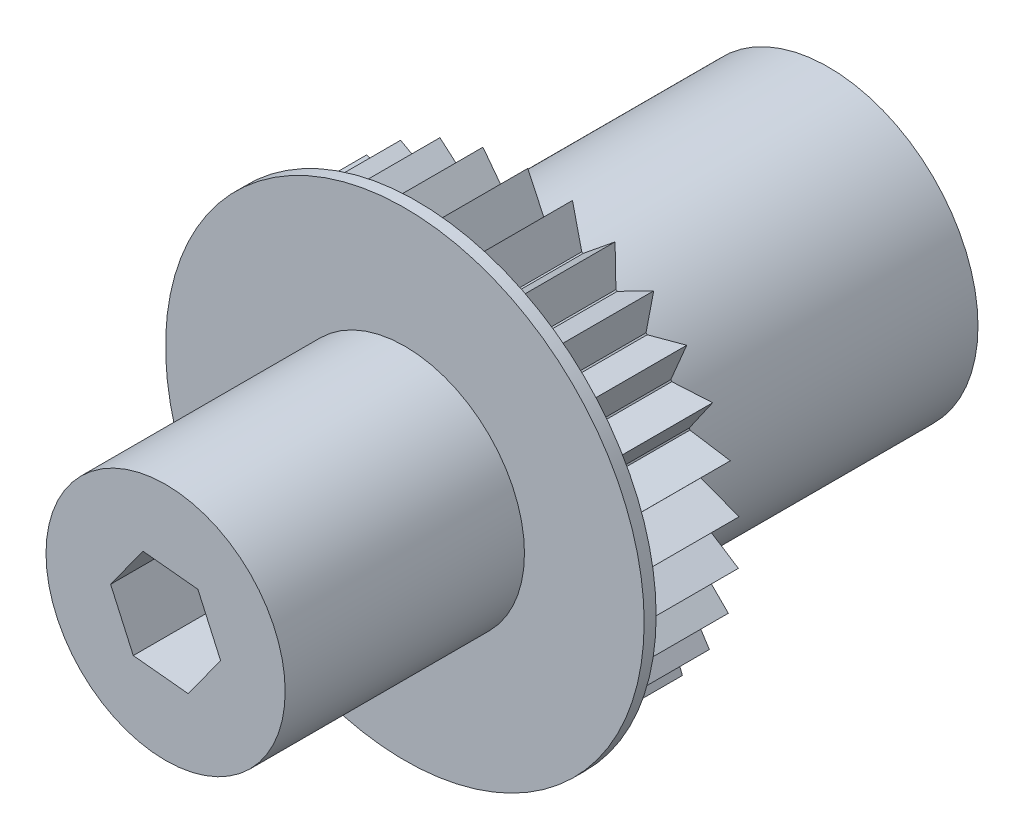
SolidWorks part; units mm, degrees
ref_plane "Front Plane" through (0, 0, 0) normal (0, 0, 1) x (1, 0, 0)
ref_plane "Top Plane" through (0, 0, 0) normal (0, 1, 0) x (1, 0, 0)
ref_plane "Right Plane" through (0, 0, 0) normal (1, 0, 0) x (0, 0, -1)
sketch "Sketch1" plane through (0, 0, 0) normal (0, 0, 1) x (1, 0, 0)
  circle A0 centre (0, 0) radius 12.5
  dimension "D1" = 25
extrude "Boss-Extrude1" add sketch "Sketch1" along normal blind 25.4
sketch "Sketch2" plane through (0, 0, 25.4) normal (0, 0, 1) x (1, 0, 0)
  circle A0 centre (0, 0) radius 9.9949
  dimension "D1" = 19.9898
extrude "Boss-Extrude2" add sketch "Sketch2" along normal blind 30
sketch "Sketch4" plane through (0, 0, 25.4) normal (0, 0, 1) x (1, 0, 0)
  line L0 (0.2712, 17.998) -> (1.7248, 14.9005)
  line L1 (-1.2752, 14.9457) -> (0.2712, 17.998)
  line L2 (1.8601, 14.8842) -> (4.0072, 17.5483)
  line L3 (4.0072, 17.5483) -> (4.7851, 14.2163)
  line L4 (4.914, 14.1722) -> (7.5681, 16.3317)
  line L5 (7.5681, 16.3317) -> (7.6363, 12.9107)
  line L6 (7.7532, 12.8408) -> (10.7983, 14.4013)
  line L7 (10.7983, 14.4013) -> (10.1537, 11.0409)
  line L8 (10.2536, 10.9483) -> (13.5565, 11.8415)
  line L9 (13.5565, 11.8415) -> (12.2274, 8.6886)
  line L10 (12.3058, 8.5772) -> (15.7223, 8.7641)
  line L11 (15.7223, 8.7641) -> (13.7666, 5.9565)
  line L12 (13.8202, 5.8312) -> (17.2009, 5.3038)
  line L13 (17.2009, 5.3038) -> (14.7042, 2.9641)
  line L14 (14.7305, 2.8304) -> (17.9277, 1.6116)
  line L15 (17.9277, 1.6116) -> (14.9992, -0.1579)
  line L16 (14.9971, -0.2941) -> (17.871, -2.151)
  line L17 (17.871, -2.151) -> (14.6386, -3.2729)
  line L18 (14.6083, -3.4057) -> (17.0333, -5.8196)
  line L19 (17.0333, -5.8196) -> (13.6382, -6.2449)
  line L20 (13.5809, -6.3685) -> (15.4511, -9.2338)
  line L21 (15.4511, -9.2338) -> (12.0418, -8.944)
  line L22 (11.9601, -9.053) -> (13.1936, -12.2445)
  line L23 (13.1936, -12.2445) -> (9.9191, -11.2522)
  line L24 (9.8165, -11.3418) -> (10.3596, -14.72)
  line L25 (10.3596, -14.72) -> (7.3629, -13.0686)
  line L26 (7.2439, -13.1349) -> (7.0727, -16.5522)
  line L27 (7.0727, -16.5522) -> (4.4849, -14.3138)
  line L28 (4.3547, -14.354) -> (3.4767, -17.661)
  line L29 (3.4767, -17.661) -> (1.4108, -14.9335)
  line L30 (1.2752, -14.9457) -> (-0.2712, -17.998)
  line L31 (-0.2712, -17.998) -> (-1.7248, -14.9005)
  line L32 (-1.8601, -14.8842) -> (-4.0072, -17.5483)
  line L33 (-4.0072, -17.5483) -> (-4.7851, -14.2163)
  line L34 (-4.914, -14.1722) -> (-7.5681, -16.3317)
  line L35 (-7.5681, -16.3317) -> (-7.6363, -12.9107)
  line L36 (-7.7532, -12.8408) -> (-10.7983, -14.4013)
  line L37 (-10.7983, -14.4013) -> (-10.1537, -11.0409)
  line L38 (-10.2536, -10.9483) -> (-13.5565, -11.8415)
  line L39 (-13.5565, -11.8415) -> (-12.2274, -8.6886)
  line L40 (-12.3058, -8.5772) -> (-15.7223, -8.7641)
  line L41 (-15.7223, -8.7641) -> (-13.7666, -5.9565)
  line L42 (-13.8202, -5.8312) -> (-17.2009, -5.3038)
  line L43 (-17.2009, -5.3038) -> (-14.7042, -2.9641)
  line L44 (-14.7305, -2.8304) -> (-17.9277, -1.6116)
  line L45 (-17.9277, -1.6116) -> (-14.9992, 0.1579)
  line L46 (-14.9971, 0.2941) -> (-17.871, 2.151)
  line L47 (-17.871, 2.151) -> (-14.6386, 3.2729)
  line L48 (-14.6083, 3.4057) -> (-17.0333, 5.8196)
  line L49 (-17.0333, 5.8196) -> (-13.6382, 6.2449)
  line L50 (-13.5809, 6.3685) -> (-15.4511, 9.2338)
  line L51 (-15.4511, 9.2338) -> (-12.0418, 8.944)
  line L52 (-11.9601, 9.053) -> (-13.1936, 12.2445)
  line L53 (-13.1936, 12.2445) -> (-9.9191, 11.2522)
  line L54 (-9.8165, 11.3418) -> (-10.3596, 14.72)
  line L55 (-10.3596, 14.72) -> (-7.3629, 13.0686)
  line L56 (-7.2439, 13.1349) -> (-7.0727, 16.5522)
  line L57 (-7.0727, 16.5522) -> (-4.4849, 14.3138)
  line L58 (-4.3547, 14.354) -> (-3.4767, 17.661)
  line L59 (-3.4767, 17.661) -> (-1.4108, 14.9335)
  circle A0 centre (0, 0) radius 15
  point P95 (0, 0)
  dimension "D3" = 30
  dimension "D1" = 3
  dimension "D4" = 18
  dimension "D2" = 30
extrude "Boss-Extrude3" add sketch "Sketch4" along normal blind 10 contours A0 | A0 L47 L46 | A0 L45 L44 | A0 L49 L48 | A0 L51 L50 | A0 L53 L52 | A0 L55 L54 | A0 L57 L56 | A0 L59 L58 | A0 L0 L1 | A0 L3 L2 | A0 L5 L4 | A0 L7 L6 | A0 L9 L8 | A0 L11 L10 | A0 L13 L12 | A0 L15 L14 | A0 L17 L16 | A0 L19 L18 | A0 L21 L20 | A0 L23 L22 | A0 L25 L24 | A0 L27 L26 | A0 L29 L28 | A0 L31 L30 | A0 L33 L32 | A0 L35 L34 | A0 L37 L36 | A0 L39 L38 | A0 L41 L40 | A0 L43 L42
sketch "Sketch5" plane through (0, 0, 35.4) normal (0, 0, 1) x (1, 0, 0)
  circle A0 centre (0, 0) radius 20
  dimension "D1" = 40
extrude "Boss-Extrude4" add sketch "Sketch5" against normal blind 1
sketch "Sketch3" plane through (0, 0, 0) normal (0, 0, -1) x (-1, 0, 0)
  line L1 (1.8966, 4.2114) -> (-2.6989, 3.7482)
  line L2 (-2.6989, 3.7482) -> (-4.5955, -0.4632)
  line L3 (-4.5955, -0.4632) -> (-1.8966, -4.2114)
  line L4 (-1.8966, -4.2114) -> (2.6989, -3.7482)
  line L5 (2.6989, -3.7482) -> (4.5955, 0.4632)
  line L6 (4.5955, 0.4632) -> (1.8966, 4.2114)
  circle A0 centre (0, 0) radius 4 construction
  dimension "D1" = 8
extrude "Cut-Extrude1" cut sketch "Sketch3" against normal through all both and the other way through all
chamfer "Chamfer1" distance 3 angle 45 6 edges at (-3.2461, 2.3373, 0) (-3.6472, -1.6425, 0) (-0.4011, -3.9798, 0) (3.2461, -2.3373, 0) (3.6472, 1.6425, 0) (0.4011, 3.9798, 0)
